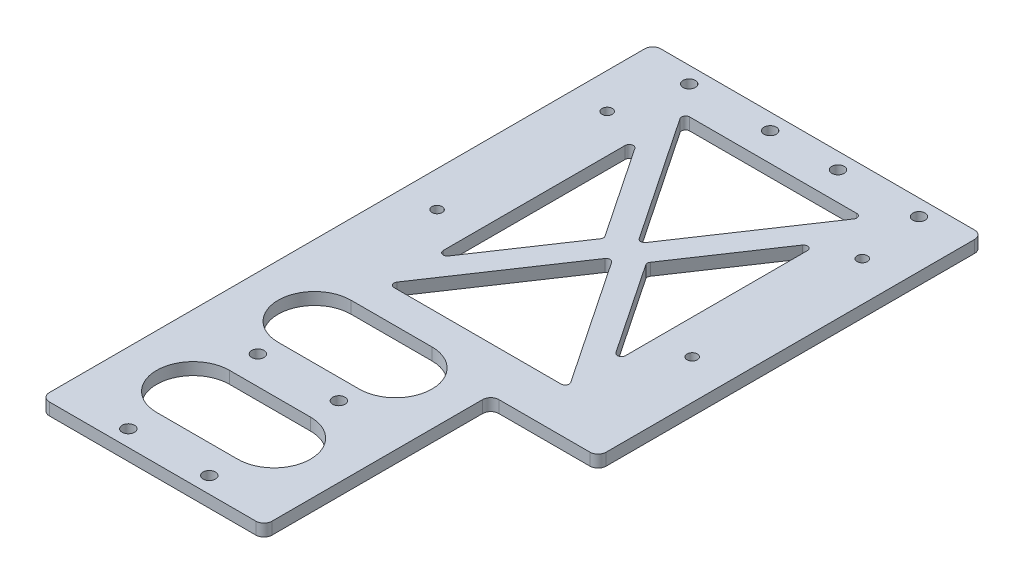
SolidWorks part; units mm, degrees
material "Thornel Mat VMA"
ref_plane "前视基准面" through (0, 0, 0) normal (0, 0, 1) x (1, 0, 0)
ref_plane "上视基准面" through (0, 0, 0) normal (0, 1, 0) x (1, 0, 0)
ref_plane "右视基准面" through (0, 0, 0) normal (1, 0, 0) x (0, 0, -1)
other "Configuration Table"
sketch "草图1" plane through (0, 0, 0) normal (0, 1, 0) x (1, 0, 0)
  line L0 (0, 0) -> (33, 0) construction
  line L1 (33, 0) -> (33, 40)
  line L2 (33, 40) -> (-55, 40)
  line L3 (-55, 40) -> (-55, -111)
  line L4 (-55, -111) -> (0, -111)
  line L5 (0, -111) -> (0, 0)
  line L6 (0, -55) -> (33, -55)
  line L7 (33, -55) -> (33, 0)
  dimension "D1" = 55
  dimension "D2" = 40
  dimension "D3" = 151
  dimension "D4" = 88
  dimension "D5" = 55
extrude "凸台-拉伸1" add sketch "草图1" along normal blind 3 contours L5 L0 L1 L2 L3 L4 | L0 L5 L6 L7
sketch "草图2" plane through (0, 3, 0) normal (0, 1, 0) x (1, 0, 0)
  line L0 (33, 40) -> (-55, 40) construction
  line L1 (-55, -111) -> (0, -111) construction
  line L2 (0, -55) -> (33, -55) construction
  line L3 (-11, 40) -> (-11, 35) construction
  line L4 (-27.5, -111) -> (-27.5, -101) construction
  line L5 (-55, 40) -> (-55, -111) construction
  circle A0 centre (-37.5, -107) radius 1.525
  circle A1 centre (-17.5, -107) radius 1.525
  circle A2 centre (-37.5, -75) radius 1.525
  circle A3 centre (-17.5, -75) radius 1.525
  circle A4 centre (-42, 36) radius 1.525
  circle A5 centre (-22, 36) radius 1.525
  circle A6 centre (-5.25, 36) radius 1.525
  circle A7 centre (14.75, 36) radius 1.525
  dimension "D1" = 3.05
  dimension "D3" = 20
  dimension "D5" = 20
  dimension "D6" = 4
  dimension "D7" = 4
  dimension "D8" = 20
  dimension "D10" = 49.75
  dimension "D12" = 13
  dimension "D2" = 20
  dimension "D4" = 20
  dimension "D9" = 5
  dimension "D11" = 10
extrude "切除-拉伸1" cut sketch "草图2" against normal through all
sketch "草图3" plane through (0, 3, 0) normal (0, 1, 0) x (1, 0, 0)
  circle A0 centre (16.75, 20) radius 1.275
  circle A1 centre (-46.25, 20) radius 1.275
  circle A2 centre (16.75, -22) radius 1.275
  circle A3 centre (-46.25, -22) radius 1.275
  dimension "D1" = 2.55
extrude "切除-拉伸2" cut sketch "草图3" against normal through all
sketch "草图5" plane through (0, 3, 0) normal (0, 1, 0) x (1, 0, 0)
  line L0 (0, -55) -> (33, -55) construction
  line L1 (33, 40) -> (26.5, 40)
  line L2 (33, 40) -> (33, -55)
  line L3 (33, -55) -> (26.5, -55)
  line L4 (26.5, 40) -> (26.5, -55)
  dimension "D1" = 6.5
extrude "切除-拉伸4" cut sketch "草图5" against normal through all
fillet "圆角3" radius 2 6 edges at (26.5, 1.5, 55) (0, 1.5, 55) (-55, 1.5, 111) (-55, 1.5, -40) (26.5, 1.5, -40) (0, 1.5, 111)
sketch "草图6" plane through (0, 3, 0) normal (0, 1, 0) x (1, 0, 0)
  line L0 (26.5, 38) -> (26.5, -53) construction
  line L1 (-39.25, -45) -> (10.75, -45) construction
  line L2 (-39.25, -45) -> (-39.25, 30) construction
  line L3 (-39.25, 30) -> (10.75, 30) construction
  line L4 (10.75, -45) -> (10.75, 30) construction
  line L5 (-39.25, -45) -> (10.75, 30) construction
  line L6 (-39.25, 30) -> (10.75, -45) construction
  line L7 (2, -55) -> (24.5, -55) construction
  line L8 (24.5, 40) -> (-53, 40) construction
  line L9 (-36.75, 29) -> (8.25, 29)
  line L10 (8.25, 29) -> (-14.25, -4.5)
  line L11 (-14.25, -4.5) -> (-36.75, 29)
  line L12 (-36.75, 18.2388) -> (-36.75, -33.2388)
  line L13 (-36.75, -33.2388) -> (-19.4628, -7.5)
  line L14 (-19.4628, -7.5) -> (-36.75, 18.2388)
  line L15 (-14.25, -7.5) -> (-14.25, -45) construction
  line L16 (-9.0372, -7.5) -> (8.25, 18.2388)
  line L17 (8.25, 18.2388) -> (8.25, -33.2388)
  line L18 (8.25, -33.2388) -> (-9.0372, -7.5)
  line L19 (-19.4628, -7.5) -> (-14.25, -7.5) construction
  line L20 (-36.75, -44) -> (8.25, -44)
  line L21 (8.25, -44) -> (-14.25, -10.5)
  line L22 (-14.25, -10.5) -> (-36.75, -44)
  point P0 (-14.25, -7.5)
  point P8 (26.5, -7.5)
  point P13 (-14.25, 40)
  point P19 (-36.75, -7.5)
  dimension "D1" = 10
  dimension "D2" = 50
  dimension "D3" = 1
  dimension "D4" = 45
  dimension "D5" = 3
  dimension "D6" = 6
extrude "切除-拉伸5" cut sketch "草图6" against normal through all both
fillet "圆角4" radius 1 12 edges at (8.25, 1.5, -29) (-14.25, 1.5, 4.5) (-36.75, 1.5, -29) (8.25, 1.5, 44) (-14.25, 1.5, 10.5) (8.25, 1.5, -18.2388) (8.25, 1.5, 33.2388) (-9.0372, 1.5, 7.5) (-36.75, 1.5, 33.2388) (-36.75, 1.5, -18.2388) (-19.4628, 1.5, 7.5) (-36.75, 1.5, 44)
sketch "草图7" plane through (0, 3, 0) normal (0, 1, 0) x (1, 0, 0)
  line L0 (-37.5, -61) -> (-17.5, -61) construction
  line L1 (-37.5, -52) -> (-17.5, -52)
  line L2 (-37.5, -70) -> (-17.5, -70)
  line L3 (-37.5, -91) -> (-17.5, -91) construction
  line L4 (-37.5, -82) -> (-17.5, -82)
  line L5 (-37.5, -100) -> (-17.5, -100)
  line L6 (-17.5, -75) -> (-17.5, -107) construction
  line L7 (-53, -111) -> (-2, -111) construction
  arc A0 (-37.5, -52) -> (-37.5, -70) centre (-37.5, -61) ccw
  arc A1 (-17.5, -70) -> (-17.5, -52) centre (-17.5, -61) ccw
  arc A2 (-37.5, -82) -> (-37.5, -100) centre (-37.5, -91) ccw
  arc A3 (-17.5, -100) -> (-17.5, -82) centre (-17.5, -91) ccw
  point P2 (-27.5, -61)
  point P7 (-27.5, -91)
  point P19 (-17.5, -91)
  point P23 (-27.5, -111)
  dimension "D2" = 9
  dimension "D4" = 9
  dimension "D1" = 20
  dimension "D3" = 12
extrude "切除-拉伸6" cut sketch "草图7" against normal through all both
